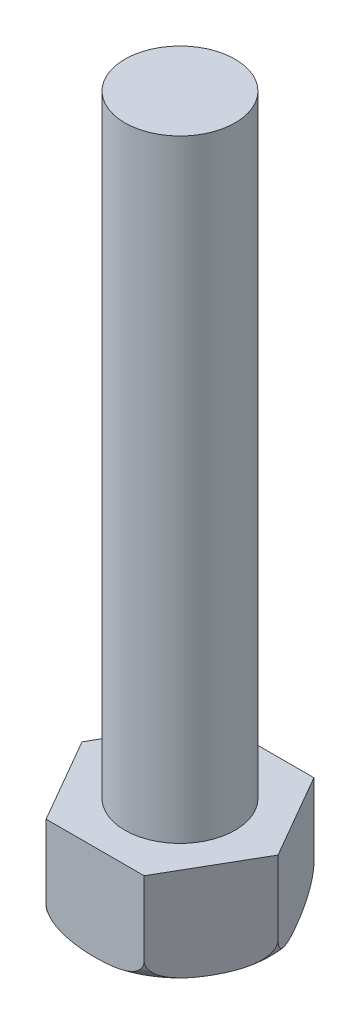
SolidWorks part; units mm, degrees
ref_plane "Front Plane" through (0, 0, 0) normal (0, 0, 1) x (1, 0, 0)
ref_plane "Top Plane" through (0, 0, 0) normal (0, 1, 0) x (1, 0, 0)
ref_plane "Right Plane" through (0, 0, 0) normal (1, 0, 0) x (0, 0, -1)
sketch "Sketch1" plane through (0, 0, 0) normal (0, 1, 0) x (1, 0, 0)
  line L1 (4, 0) -> (2, 3.4641)
  line L2 (2, 3.4641) -> (-2, 3.4641)
  line L3 (-2, 3.4641) -> (-4, 0)
  line L4 (-4, 0) -> (-2, -3.4641)
  line L5 (-2, -3.4641) -> (2, -3.4641)
  line L6 (2, -3.4641) -> (4, 0)
  circle A0 centre (0, 0) radius 3.4641 construction
  dimension "D1" = 8
extrude "Boss-Extrude1" add sketch "Sketch1" along normal mid plane 4
sketch "Sketch2" plane through (0, 2, 0) normal (0, 1, 0) x (1, 0, 0)
  circle A0 centre (0, 0) radius 2.25
extrude "Boss-Extrude2" add sketch "Sketch2" along normal blind 25
sketch "Sketch3" plane through (0, 0, 0) normal (0, 0, 1) x (1, 0, 0)
  line L0 (2.2489, -2) -> (3, -2)
  line L1 (2, -2) -> (4, -2) construction
  line L2 (4, -1) -> (4, -0.8127)
  line L3 (4, 2) -> (4, -2) construction
  line L4 (4, -0.8127) -> (5.5944, -2.2686)
  line L5 (5.5944, -2.2686) -> (3.3508, -3.2731)
  line L6 (3.3508, -3.2731) -> (2.2489, -2)
  line L7 (0, -2) -> (0, -3.1499) construction
  line L8 (-2, -2) -> (2, -2) construction
  arc A0 (3, -2) -> (4, -1) centre (3, -1) ccw
  point P12 (4, -2)
  dimension "D1" = 1
revolve "Cut-Revolve1" cut sketch "Sketch3" angle 360 about L7
